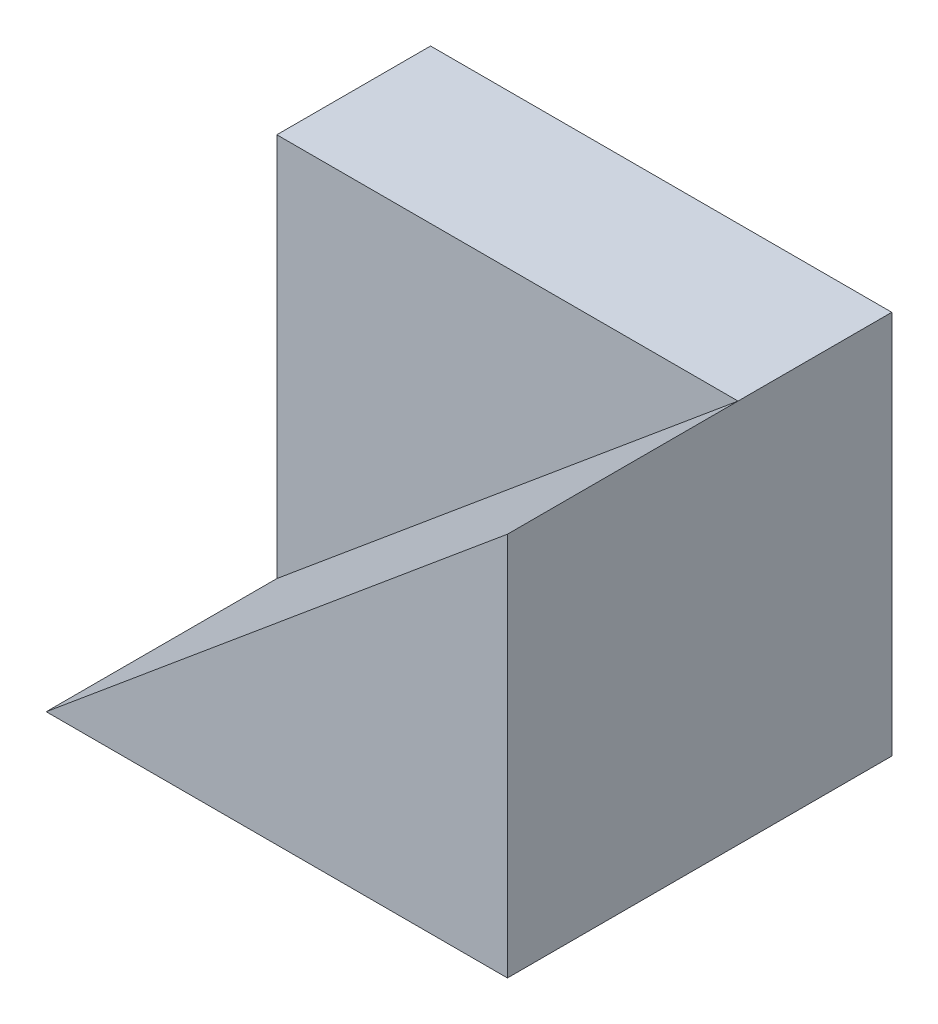
SolidWorks part; units mm, degrees
ref_plane "Front Plane" through (0, 0, 0) normal (0, 0, 1) x (1, 0, 0)
ref_plane "Top Plane" through (0, 0, 0) normal (0, 1, 0) x (1, 0, 0)
ref_plane "Right Plane" through (0, 0, 0) normal (1, 0, 0) x (0, 0, -1)
sketch "Sketch1" plane through (0, 0, 0) normal (0, 0, 1) x (1, 0, 0)
  line L0 (-30, 25) -> (0, 25)
  line L1 (0, 25) -> (0, 0)
  line L2 (0, 0) -> (-30, 0)
  line L3 (-30, 0) -> (-30, 25)
  dimension "D1" = 30
  dimension "D2" = 25
extrude "Boss-Extrude1" add sketch "Sketch1" along normal blind 10
sketch "Sketch2" plane through (0, 0, 10) normal (0, 0, 1) x (1, 0, 0)
  line L0 (-30, 0) -> (0, 25)
  line L1 (0, 25) -> (0, 0)
  line L2 (0, 0) -> (-30, 0)
extrude "Boss-Extrude2" add sketch "Sketch2" along normal blind 15
